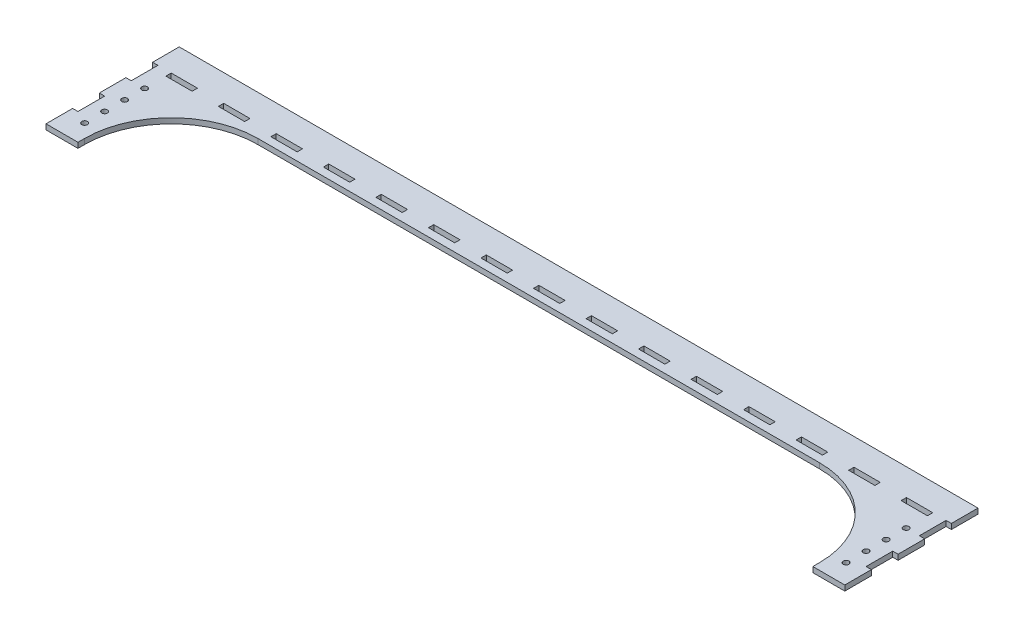
SolidWorks part; units mm, degrees
ref_plane "Front Plane" through (0, 0, 0) normal (0, 0, 1) x (1, 0, 0)
ref_plane "Top Plane" through (0, 0, 0) normal (0, 1, 0) x (1, 0, 0)
ref_plane "Right Plane" through (0, 0, 0) normal (1, 0, 0) x (0, 0, -1)
sketch "Sketch1" plane through (0, 0, 0) normal (0, 1, 0) x (1, 0, 0)
  line L0 (0, -26.4292) -> (0, 52.5615) construction
  line L1 (299.8, 24) -> (299.8, 4)
  line L2 (285.8, -44.149) -> (285.8, -73.2727) construction
  line L3 (299.8, -76) -> (275.8, -76)
  line L4 (275.8, -76) -> (275.8, -71)
  line L5 (210.8, -6) -> (-210.8, -6)
  line L6 (-9.8625, 0) -> (9.8625, 0)
  line L7 (9.8625, 0) -> (9.8625, 4)
  line L8 (9.8625, 4) -> (-9.8625, 4)
  line L9 (29.5875, 4) -> (29.5875, 0)
  line L10 (29.5875, 0) -> (49.3125, 0)
  line L11 (49.3125, 0) -> (49.3125, 4)
  line L12 (49.3125, 4) -> (29.5875, 4)
  line L13 (88.7325, 4) -> (69.0075, 4)
  line L14 (69.0075, 4) -> (69.0075, 0)
  line L15 (69.0075, 0) -> (88.7325, 0)
  line L16 (88.7325, 0) -> (88.7325, 4)
  line L17 (128.1525, 4) -> (108.4275, 4)
  line L18 (108.4275, 4) -> (108.4275, 0)
  line L19 (108.4275, 0) -> (128.1525, 0)
  line L20 (128.1525, 0) -> (128.1525, 4)
  line L21 (167.5725, 4) -> (147.8475, 4)
  line L22 (147.8475, 4) -> (147.8475, 0)
  line L23 (147.8475, 0) -> (167.5725, 0)
  line L24 (167.5725, 0) -> (167.5725, 4)
  line L25 (206.9925, 4) -> (187.2675, 4)
  line L26 (187.2675, 4) -> (187.2675, 0)
  line L27 (187.2675, 0) -> (206.9925, 0)
  line L28 (206.9925, 0) -> (206.9925, 4)
  line L29 (246.4125, 4) -> (226.6875, 4)
  line L30 (226.6875, 4) -> (226.6875, 0)
  line L31 (226.6875, 0) -> (246.4125, 0)
  line L32 (246.4125, 0) -> (246.4125, 4)
  line L33 (285.8325, 4) -> (266.1075, 4)
  line L34 (266.1075, 4) -> (266.1075, 0)
  line L35 (266.1075, 0) -> (285.8325, 0)
  line L36 (285.8325, 0) -> (285.8325, 4)
  line L37 (299.8, 4) -> (295.8, 4)
  line L38 (295.8, 4) -> (295.8, -16)
  line L39 (299.8, 24) -> (-299.8, 24)
  line L40 (295.8, -16) -> (299.8, -16)
  line L41 (299.8, -16) -> (299.8, -36)
  line L42 (299.8, -36) -> (295.8, -36)
  line L43 (295.8, -36) -> (295.8, -56)
  line L44 (295.8, -56) -> (299.8, -56)
  line L45 (299.8, -56) -> (299.8, -76)
  line L46 (-285.8, -44.149) -> (-285.8, -73.2727) construction
  line L47 (-299.8, -56) -> (-299.8, -76)
  line L48 (-295.8, -56) -> (-299.8, -56)
  line L49 (-295.8, -36) -> (-295.8, -56)
  line L50 (-299.8, -36) -> (-295.8, -36)
  line L51 (-299.8, -16) -> (-299.8, -36)
  line L52 (-295.8, -16) -> (-299.8, -16)
  line L53 (-295.8, 4) -> (-295.8, -16)
  line L54 (-299.8, 4) -> (-295.8, 4)
  line L55 (-285.8325, 0) -> (-285.8325, 4)
  line L56 (-266.1075, 0) -> (-285.8325, 0)
  line L57 (-266.1075, 4) -> (-266.1075, 0)
  line L58 (-285.8325, 4) -> (-266.1075, 4)
  line L59 (-246.4125, 0) -> (-246.4125, 4)
  line L60 (-226.6875, 0) -> (-246.4125, 0)
  line L61 (-226.6875, 4) -> (-226.6875, 0)
  line L62 (-246.4125, 4) -> (-226.6875, 4)
  line L63 (-206.9925, 0) -> (-206.9925, 4)
  line L64 (-187.2675, 0) -> (-206.9925, 0)
  line L65 (-187.2675, 4) -> (-187.2675, 0)
  line L66 (-206.9925, 4) -> (-187.2675, 4)
  line L67 (-167.5725, 0) -> (-167.5725, 4)
  line L68 (-147.8475, 0) -> (-167.5725, 0)
  line L69 (-147.8475, 4) -> (-147.8475, 0)
  line L70 (-167.5725, 4) -> (-147.8475, 4)
  line L71 (-128.1525, 0) -> (-128.1525, 4)
  line L72 (-108.4275, 0) -> (-128.1525, 0)
  line L73 (-108.4275, 4) -> (-108.4275, 0)
  line L74 (-128.1525, 4) -> (-108.4275, 4)
  line L75 (-88.7325, 0) -> (-88.7325, 4)
  line L76 (-69.0075, 0) -> (-88.7325, 0)
  line L77 (-69.0075, 4) -> (-69.0075, 0)
  line L78 (-88.7325, 4) -> (-69.0075, 4)
  line L79 (-49.3125, 4) -> (-29.5875, 4)
  line L80 (-49.3125, 0) -> (-49.3125, 4)
  line L81 (-29.5875, 0) -> (-49.3125, 0)
  line L82 (-29.5875, 4) -> (-29.5875, 0)
  line L83 (-9.8625, 0) -> (-9.8625, 4)
  line L84 (-275.8, -76) -> (-275.8, -71)
  line L85 (-299.8, -76) -> (-275.8, -76)
  line L86 (-299.8, 24) -> (-299.8, 4)
  line L87 (258.2275, -38.5) -> (311.1408, -38.5) construction
  circle A0 centre (285.8, -61) radius 2.125
  circle A1 centre (285.8, -46) radius 2.125
  circle A2 centre (-285.8, -46) radius 2.125
  circle A3 centre (-285.8, -61) radius 2.125
  arc A4 (275.8, -71) -> (210.8, -6) centre (210.8, -71) ccw
  arc A5 (-275.8, -71) -> (-210.8, -6) centre (-210.8, -71) cw
  circle A6 centre (285.8, -16) radius 2.125
  circle A7 centre (285.8, -31) radius 2.125
  circle A8 centre (-285.8, -31) radius 2.125
  circle A9 centre (-285.8, -16) radius 2.125
  point P69 (0, 24)
  point P100 (0, 4)
  point P101 (0, 0)
  point P102 (0, -6)
  point P105 (275.8, -6)
  point P108 (-275.8, -6)
  dimension "D11" = 4.25
  dimension "D17" = 65
  dimension "D1" = 24
  dimension "D2" = 10
  dimension "D3" = 299.8
  dimension "D4" = 24
  dimension "D5" = 6
  dimension "D6" = 9.8625
  dimension "D7" = 4
  dimension "D8" = 19.725
  dimension "D9" = 19.725
  dimension "D12" = 15
  dimension "D13" = 15
  dimension "D14" = 100
  dimension "D15" = 20
  dimension "D16" = 4
  dimension "D18" = 7.5
  dimension "D10" = 7
extrude "Boss-Extrude1" add sketch "Sketch1" along normal blind 4
